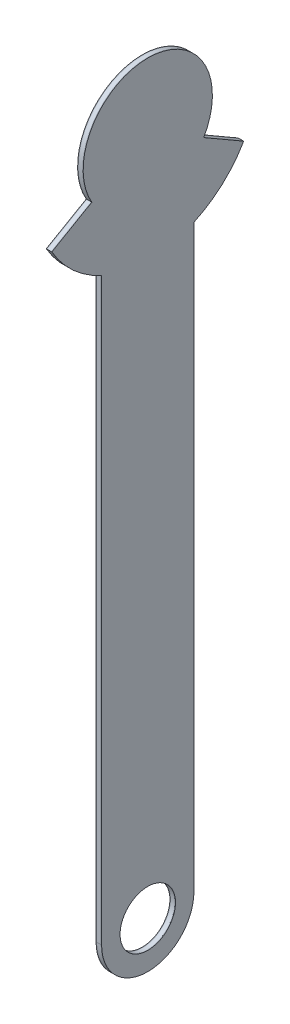
SolidWorks part; units mm, degrees
ref_plane "Front Plane" through (0, 0, 0) normal (0, 0, 1) x (1, 0, 0)
ref_plane "Top Plane" through (0, 0, 0) normal (0, 1, 0) x (1, 0, 0)
ref_plane "Right Plane" through (0, 0, 0) normal (1, 0, 0) x (0, 0, -1)
sketch "Sketch2" plane through (0, 0, 0) normal (1, 0, 0) x (0, 0, -1)
  line L0 (0, -196.8) -> (0, 196.8) construction
  line L2 (-30.3109, 179.3) -> (-51.9615, 166.8)
  line L3 (30.3109, 179.3) -> (51.9615, 166.8)
  line L9 (-25, 142.2564) -> (-25, -171.8)
  line L10 (25, 142.2564) -> (25, -171.8)
  circle A0 centre (0, 196.8) radius 35
  arc A1 (-51.9615, 166.8) -> (51.9615, 166.8) centre (0, 196.8) ccw
  arc A2 (-25, -171.8) -> (25, -171.8) centre (0, -171.8) ccw
  circle A3 centre (0, -171.8) radius 15
  point P4 (0, 0)
  point P15 (0, 196.8)
  dimension "D2" = 70
  dimension "D3" = 120
  dimension "D7" = 50
  dimension "D8" = 30
  dimension "D1" = 393.6
extrude "Boss-Extrude1" add sketch "Sketch2" along normal blind 0.25
sketch "Sketch3" plane through (0, 0, 0) normal (-1, 0, 0) x (0, 0, 1)
  circle A3 centre (0, -171.8) radius 15
  circle A4 centre (0, -171.8) radius 15
  circle M10 centre (0, -171.8) radius 15
  arc M11 (30.3109, 179.3) -> (-30.3109, 179.3) centre (0, 196.8) ccw
  line M12 (-30.3109, 179.3) -> (-51.9615, 166.8)
  arc M13 (-51.9615, 166.8) -> (-25, 142.2564) centre (0, 196.8) ccw
  line M14 (-25, 142.2564) -> (-25, -171.8)
  arc M15 (-25, -171.8) -> (25, -171.8) centre (0, -171.8) ccw
  line M16 (25, -171.8) -> (25, 142.2564)
  arc M17 (25, 142.2564) -> (51.9615, 166.8) centre (0, 196.8) ccw
  line M18 (51.9615, 166.8) -> (30.3109, 179.3)
  dimension "D1" = 0
extrude "Boss-Extrude2" add sketch "Sketch3" along normal blind 2.5 separate body contours M18 M11 M12 M13 M14 M15 M16 M17 M10
sketch "Sketch4" plane through (-2.5, 0, 0) normal (-1, 0, 0) x (0, 0, 1)
  circle A1 centre (0, -171.8) radius 15
  circle A2 centre (0, -171.8) radius 15
  line M2 (51.9615, 166.8) -> (30.3109, 179.3)
  arc M3 (30.3109, 179.3) -> (-30.3109, 179.3) centre (0, 196.8) ccw
  line M4 (-30.3109, 179.3) -> (-51.9615, 166.8)
  arc M5 (-51.9615, 166.8) -> (-25, 142.2564) centre (0, 196.8) ccw
  line M6 (-25, 142.2564) -> (-25, -171.8)
  arc M7 (-25, -171.8) -> (25, -171.8) centre (0, -171.8) ccw
  line M8 (25, -171.8) -> (25, 142.2564)
  arc M9 (25, 142.2564) -> (51.9615, 166.8) centre (0, 196.8) ccw
  circle M10 centre (0, -171.8) radius 15
  dimension "D1" = 0
extrude "Boss-Extrude3" add sketch "Sketch4" along normal blind 0.25 separate body contours M9 M2 M3 M4 M5 M6 M7 M8 M10
sketch "Sketch5" plane through (0.25, 0, 0) normal (1, 0, 0) x (0, 0, -1)
  circle A0 centre (0, 196.8) radius 17.5 construction
  circle A1 centre (0, 196.8) radius 12 construction
  point P4 (0, 208.8)
  point P7 (11.4127, 200.5082)
  point P8 (7.0534, 187.0918)
  point P9 (-7.0534, 187.0918)
  point P10 (-11.4127, 200.5082)
  dimension "D1" = 35
  dimension "D2" = 24
  dimension "D3" = 5
